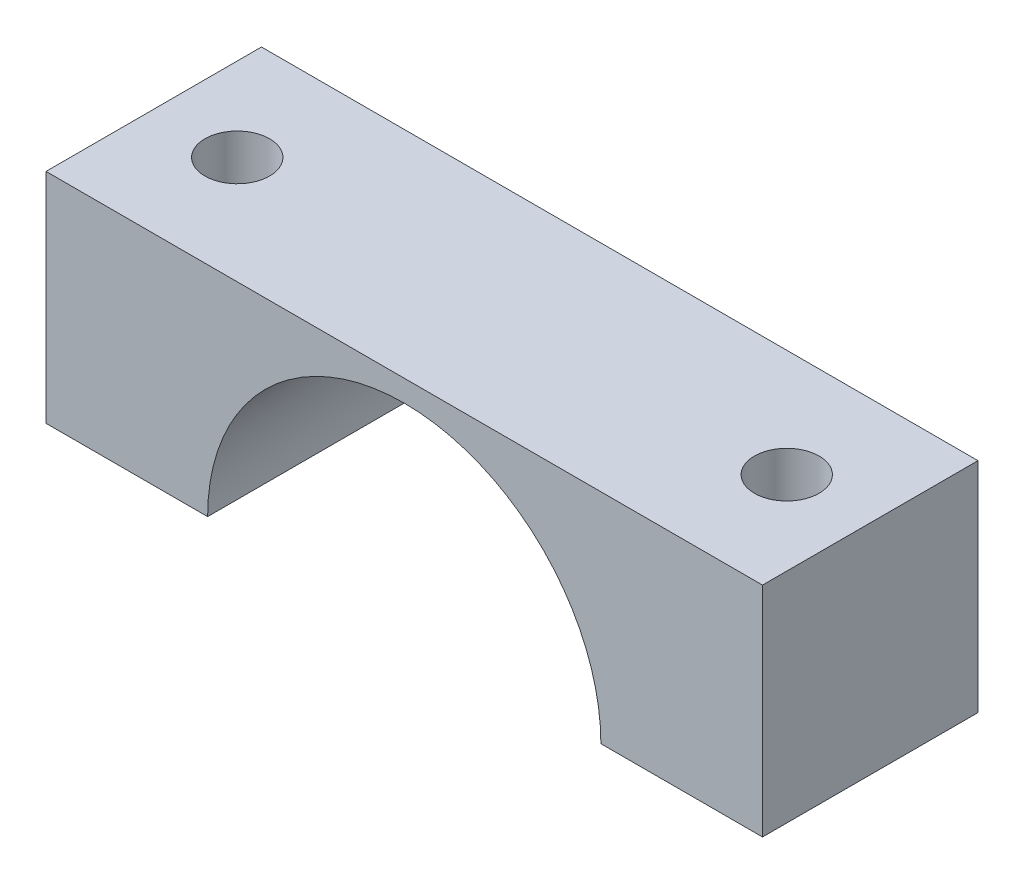
SolidWorks part; units mm, degrees
ref_plane "Front Plane" through (0, 0, 0) normal (0, 0, 1) x (1, 0, 0)
ref_plane "Top Plane" through (0, 0, 0) normal (0, 1, 0) x (1, 0, 0)
ref_plane "Right Plane" through (0, 0, 0) normal (1, 0, 0) x (0, 0, -1)
sketch "草图1" plane through (0, 0, 0) normal (0, 0, 1) x (1, 0, 0)
  line L0 (-33.25, 0) -> (-18.25, 0)
  line L1 (-33.25, 0) -> (-33.25, 20.25)
  line L3 (-33.25, 20.25) -> (33.25, 20.25)
  line L5 (33.25, 20.25) -> (33.25, 0)
  line L6 (18.25, 0) -> (33.25, 0)
  arc A1 (18.25, 0) -> (-18.25, 0) centre (0, 0) ccw
  point P1 (-33.25, 20.25)
  point P8 (33.25, 20.25)
  point P9 (33.0453, 20.25)
  point P10 (-32.9507, 20.25)
  dimension "D1" = 36.5
  dimension "D2" = 15
  dimension "D4" = 2
extrude "凸台-拉伸1" add sketch "草图1" along normal blind 20
sketch "草图2" plane through (0, 20.25, 0) normal (0, 1, 0) x (1, 0, 0)
  line L0 (-37.4303, -10) -> (47.973, -10) construction
  line L1 (33.25, 0) -> (-33.25, 0) construction
  line L2 (0, 9.6014) -> (0, -29.6735) construction
  circle A0 centre (-25.5, -10) radius 3
  circle A1 centre (25.5, -10) radius 3
  dimension "D4" = 6
  dimension "D1" = 10
  dimension "D2" = 25.5
  dimension "D3" = 25.5
extrude "切除-拉伸1" cut sketch "草图2" against normal through all
